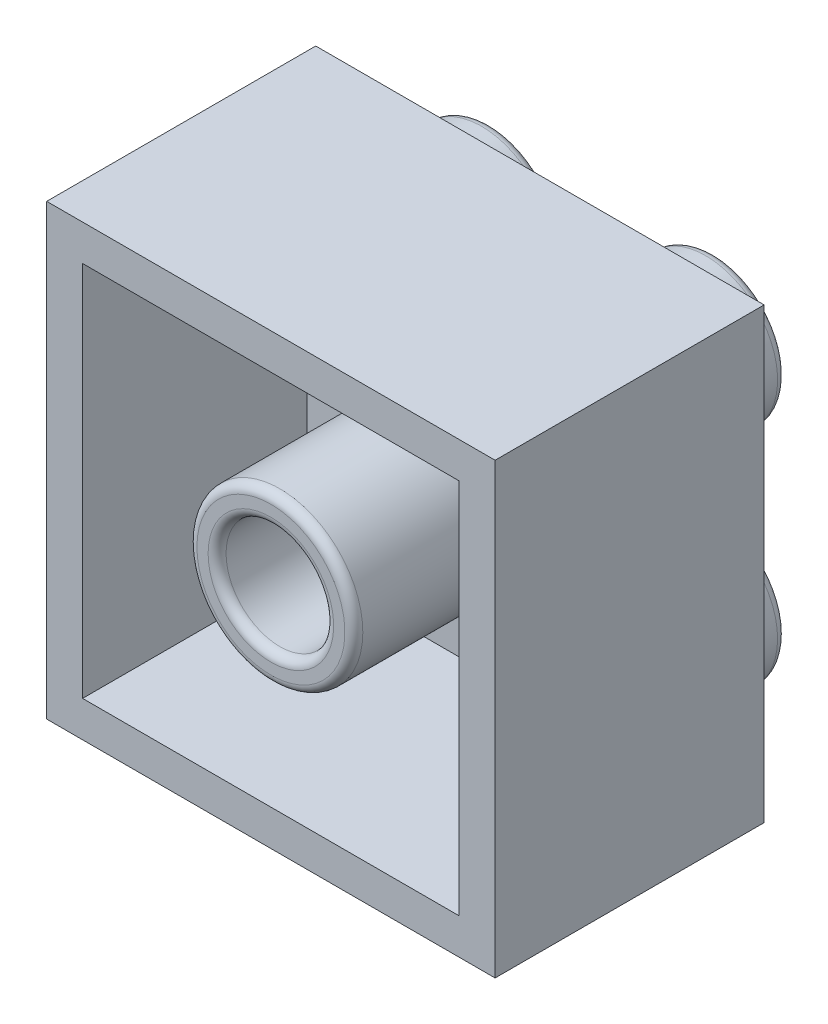
SolidWorks part; units mm, degrees
ref_plane "Plan de face" through (0, 0, 0) normal (0, 0, 1) x (1, 0, 0)
ref_plane "Plan de dessus" through (0, 0, 0) normal (0, 1, 0) x (1, 0, 0)
ref_plane "Plan de droite" through (0, 0, 0) normal (1, 0, 0) x (0, 0, -1)
sketch "Esquisse2" plane through (0, 0, 0) normal (0, 0, 1) x (1, 0, 0)
  line L0 (-80.0595, 0) -> (82.1429, 0) construction
  line L1 (0, 50) -> (0, -50) construction
  line L2 (-50, 50) -> (50, 50)
  line L3 (50, 50) -> (50, -50)
  line L4 (50, -50) -> (-50, -50)
  line L5 (-50, -50) -> (-50, 50)
  line L6 (-50, 50) -> (50, 50)
  dimension "D1" = 100
extrude "Boss.-Extru.1" add sketch "Esquisse2" along normal blind 60 contours L5 L2 L3 L4
sketch "Esquisse3" plane through (0, 0, 0) normal (0, 0, -1) x (-1, 0, 0)
  line L0 (50, 0) -> (-50, 0) construction
  line L1 (50, -50) -> (50, 50) construction
  line L2 (-50, 50) -> (-50, -50) construction
  line L3 (0, -50) -> (0, 50) construction
  line L4 (-50, -50) -> (50, -50) construction
  line L5 (50, 50) -> (-50, 50) construction
  line L6 (50, -50) -> (0, 0) construction
  line L7 (0, 0) -> (-50, -50) construction
  line L8 (0, 0) -> (-50, 50) construction
  line L9 (0, 0) -> (50, 50) construction
  circle A4 centre (-25, 25) radius 16
  circle A5 centre (-25, -25) radius 16
  circle A6 centre (25, 25) radius 16
  circle A7 centre (25, -25) radius 16
  dimension "D4" = 32
extrude "Boss.-Extru.3" add sketch "Esquisse3" along normal blind 14
sketch "Esquisse4" plane through (0, 0, 60) normal (0, 0, 1) x (1, 0, 0)
  line L0 (-50, 0) -> (50, 0) construction
  line L3 (-50, -50) -> (-50, 50) construction
  line L4 (50, 50) -> (50, -50) construction
  line L5 (0, 50) -> (0, -50) construction
  line L6 (-50, 50) -> (50, 50) construction
  line L7 (50, -50) -> (-50, -50) construction
  line L8 (-42, -42) -> (-42, 42)
  line L9 (-42, 42) -> (42, 42)
  line L10 (42, 42) -> (42, -42)
  line L11 (42, -42) -> (-42, -42)
  circle A0 centre (0, 0) radius 12
  circle A2 centre (0, 0) radius 18.5
  dimension "D2" = 24
  dimension "D3" = 37
  dimension "D1" = 8
extrude "Enlèv. mat.-Extru.1" cut sketch "Esquisse4" against normal blind 50 contours L11 L10 L9 L8 A2 | A0
fillet "Congé2" radius 2 12 edges at (12, 0, 10) (12, 0, 60) (18.5, 0, 60) (18.5, 0, 10) (-9, 25, 0) (-9, 25, -14) (9, 25, 0) (9, 25, -14) (-41, -25, 0) (-41, -25, -14) (41, -25, 0) (41, -25, -14)
